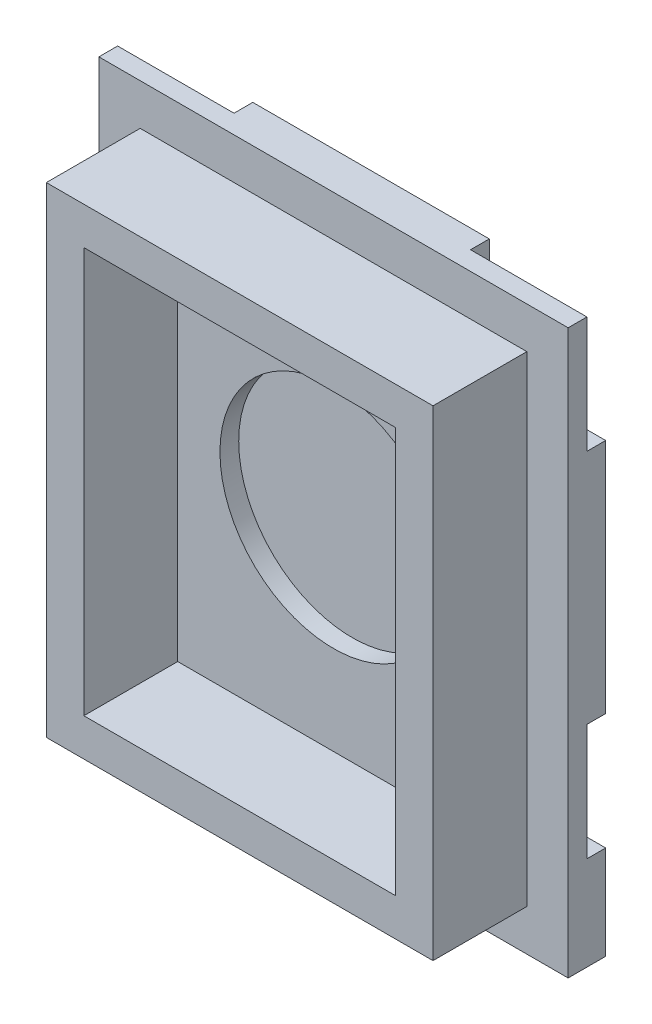
SolidWorks part; units mm, degrees
ref_plane "正面" through (0, 0, 0) normal (0, 0, 1) x (1, 0, 0)
ref_plane "平面" through (0, 0, 0) normal (0, 1, 0) x (1, 0, 0)
ref_plane "右側面" through (0, 0, 0) normal (1, 0, 0) x (0, 0, -1)
sketch "ｽｹｯﾁ1" plane through (0, 0, 0) normal (0, 0, 1) x (1, 0, 0)
  line L1 (-36.7373, 39.7071) -> (-11.7373, 39.7071)
  line L2 (-36.7373, 39.7071) -> (-36.7373, 9.7071)
  line L3 (-36.7373, 9.7071) -> (-11.7373, 9.7071)
  line L4 (-11.7373, 39.7071) -> (-11.7373, 9.7071)
  dimension "D3" = 25
  dimension "D4" = 30
extrude "ﾎﾞｽ - 押し出し1" add sketch "ｽｹｯﾁ1" along normal blind 2
sketch "ｽｹｯﾁ2" plane through (0, 0, 2) normal (0, 0, 1) x (1, 0, 0)
  line L0 (-11.7373, 39.7071) -> (-36.7373, 39.7071) construction
  line L1 (-13.9373, 37.5071) -> (-34.5373, 37.5071)
  line L2 (-13.9373, 37.5071) -> (-13.9373, 11.9071)
  line L3 (-13.9373, 11.9071) -> (-34.5373, 11.9071)
  line L4 (-34.5373, 37.5071) -> (-34.5373, 11.9071)
  line L5 (-36.7373, 9.7071) -> (-11.7373, 9.7071) construction
  line L6 (-36.7373, 39.7071) -> (-36.7373, 9.7071) construction
  line L7 (-11.7373, 9.7071) -> (-11.7373, 39.7071) construction
  dimension "D2" = 2.2
  dimension "D3" = 2.2
  dimension "D4" = 2.2
  dimension "D5" = 2.2
extrude "ﾎﾞｽ - 押し出し2" add sketch "ｽｹｯﾁ2" along normal blind 5
sketch "ｽｹｯﾁ3" plane through (0, 0, 7) normal (0, 0, 1) x (1, 0, 0)
  line L0 (-13.9373, 37.5071) -> (-34.5373, 37.5071) construction
  line L1 (-32.5373, 13.9071) -> (-15.9373, 13.9071)
  line L2 (-32.5373, 13.9071) -> (-32.5373, 35.5071)
  line L3 (-32.5373, 35.5071) -> (-15.9373, 35.5071)
  line L4 (-15.9373, 13.9071) -> (-15.9373, 35.5071)
  line L5 (-34.5373, 11.9071) -> (-13.9373, 11.9071) construction
  line L6 (-13.9373, 11.9071) -> (-13.9373, 37.5071) construction
  line L7 (-34.5373, 37.5071) -> (-34.5373, 11.9071) construction
  dimension "D1" = 21.6
  dimension "D2" = 16.6
  dimension "D3" = 2
  dimension "D4" = 2
  dimension "D5" = 2
  dimension "D6" = 2
extrude "ｶｯﾄ - 押し出し1" cut sketch "ｽｹｯﾁ3" against normal blind 5
sketch "ｽｹｯﾁ4" plane through (0, 0, 0) normal (0, 0, -1) x (-1, 0, 0)
  line L0 (11.7373, 39.7071) -> (36.7373, 39.7071) construction
  line L1 (11.7373, 39.7071) -> (17.9373, 39.7071)
  line L2 (11.7373, 39.7071) -> (11.7373, 33.5071)
  line L3 (11.7373, 33.5071) -> (17.9373, 33.5071)
  line L4 (17.9373, 39.7071) -> (17.9373, 33.5071)
  line L5 (36.7373, 39.7071) -> (30.5373, 39.7071)
  line L6 (36.7373, 39.7071) -> (36.7373, 33.5071)
  line L7 (36.7373, 33.5071) -> (30.5373, 33.5071)
  line L8 (30.5373, 39.7071) -> (30.5373, 33.5071)
  line L9 (36.7373, 14.7071) -> (30.5373, 14.7071)
  line L10 (36.7373, 14.7071) -> (36.7373, 20.9071)
  line L11 (36.7373, 20.9071) -> (30.5373, 20.9071)
  line L12 (30.5373, 14.7071) -> (30.5373, 20.9071)
  line L13 (11.7373, 14.7071) -> (17.9373, 14.7071)
  line L14 (11.7373, 14.7071) -> (11.7373, 20.9071)
  line L15 (11.7373, 20.9071) -> (17.9373, 20.9071)
  line L16 (17.9373, 14.7071) -> (17.9373, 20.9071)
  line L17 (36.7373, 39.7071) -> (36.7373, 9.7071) construction
  point P16 (0, 0)
  point P22 (0, 0)
  point P24 (0, 0)
  dimension "D1" = 6.2
  dimension "D2" = 6.2
  dimension "D3" = 6.2
  dimension "D4" = 6.2
  dimension "D5" = 6.2
  dimension "D6" = 6.2
  dimension "D7" = 6.2
  dimension "D8" = 25
  dimension "D9" = 25
extrude "ｶｯﾄ - 押し出し2" cut sketch "ｽｹｯﾁ4" against normal blind 1
sketch "ｽｹｯﾁ5" plane through (0, 0, 2) normal (0, 0, 1) x (1, 0, 0)
  line L0 (-36.7373, 39.7071) -> (-36.7373, 9.7071) construction
  line L1 (-11.7373, 39.7071) -> (-36.7373, 39.7071) construction
  circle A0 centre (-24.2373, 24.7071) radius 6.05
  dimension "D1" = 12.1
  dimension "D2" = 12.5
  dimension "D3" = 15
extrude "ｶｯﾄ - 押し出し3" cut sketch "ｽｹｯﾁ5" against normal blind 1
